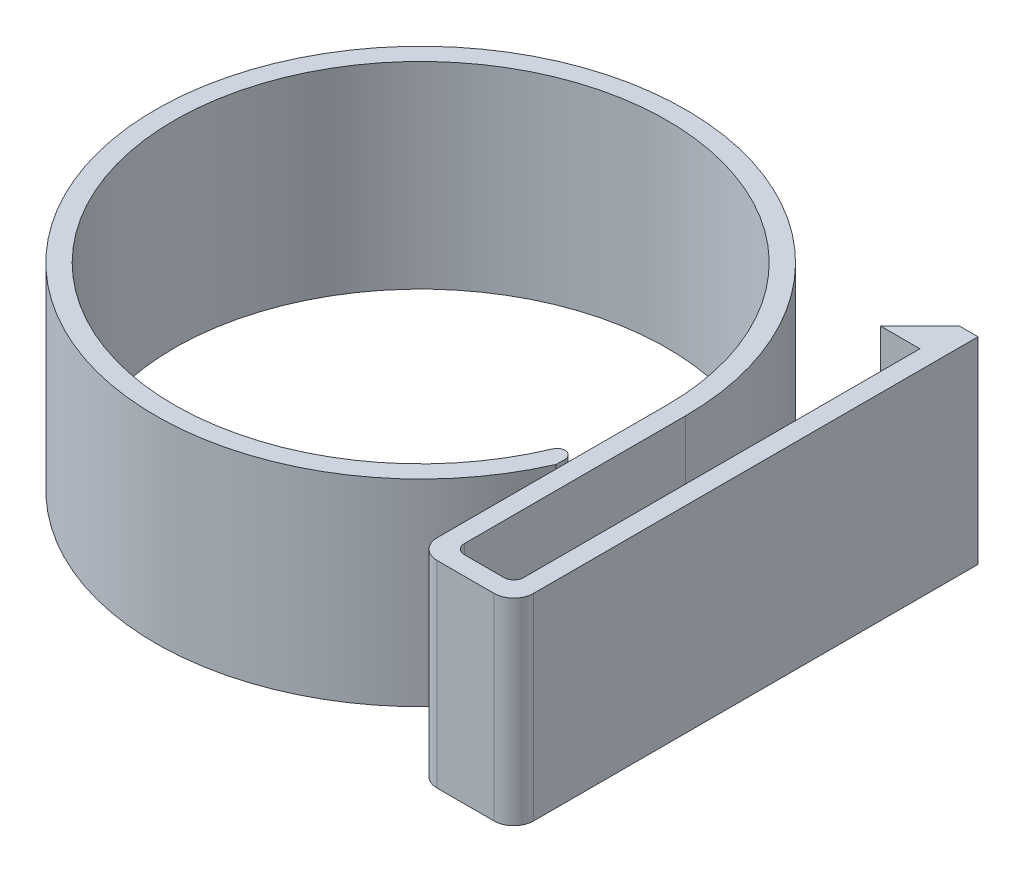
SolidWorks part; units mm, degrees
ref_plane "Front Plane" through (0, 0, 0) normal (0, 0, 1) x (1, 0, 0)
ref_plane "Top Plane" through (0, 0, 0) normal (0, 1, 0) x (1, 0, 0)
ref_plane "Right Plane" through (0, 0, 0) normal (1, 0, 0) x (0, 0, -1)
sketch "Sketch1" plane through (0, 0, 0) normal (0, 1, 0) x (1, 0, 0)
  line L0 (17.075, 0) -> (17.075, -14.8854)
  line L1 (15.875, 0) -> (15.875, -16.0854)
  line L2 (15.875, -16.0854) -> (22.085, -16.0854)
  line L3 (15.621, -6.8949) -> (15.621, -2.8284)
  line L4 (22.085, -16.0854) -> (22.085, 10.5146)
  line L5 (22.085, 10.5146) -> (20.885, 10.5146) construction
  line L6 (20.885, 10.5146) -> (20.885, -14.8854)
  line L7 (20.885, -14.8854) -> (17.075, -14.8854)
  line L8 (20.885, 11.2766) -> (18.345, 11.2766)
  line L10 (20.885, 11.2766) -> (20.885, 10.5146)
  line L11 (20.885, 10.5146) -> (22.085, 10.5146) construction
  line L13 (18.345, 11.2766) -> (20.885, 13.8166)
  line L14 (22.085, 13.8166) -> (22.085, 10.5146)
  line L15 (20.885, 13.8166) -> (22.085, 13.8166)
  arc A0 (15.875, 0) -> (15.621, -2.8284) centre (0, 0) ccw
  arc A1 (17.075, 0) -> (15.621, -6.8949) centre (0, 0) ccw
  point P13 (20.885, 13.5787)
  dimension "D1" = 31.75
  dimension "D2" = 1.2
  dimension "D3" = 0.254
  dimension "D4" = 14.8854
  dimension "D5" = 1.2
  dimension "D6" = 1.2
  dimension "D7" = 25.4
  dimension "D8" = 3.81
  dimension "D9" = 0.762
  dimension "D10" = 45
  dimension "D11" = 2.54
extrude "Boss-Extrude1" add sketch "Sketch1" along normal blind 12.7
fillet "Fillet2" radius 0.635 2 edges at (20.885, 6.35, 14.8854) (17.075, 6.35, 14.8854)
fillet "Fillet3" radius 1.27 2 edges at (22.085, 6.35, 16.0854) (15.875, 6.35, 16.0854)
fillet "Fillet4" radius 0.508 1 edges at (15.621, 6.35, 2.8284)
equation "\"D5@Sketch1\"=\"D2@Sketch1\""
